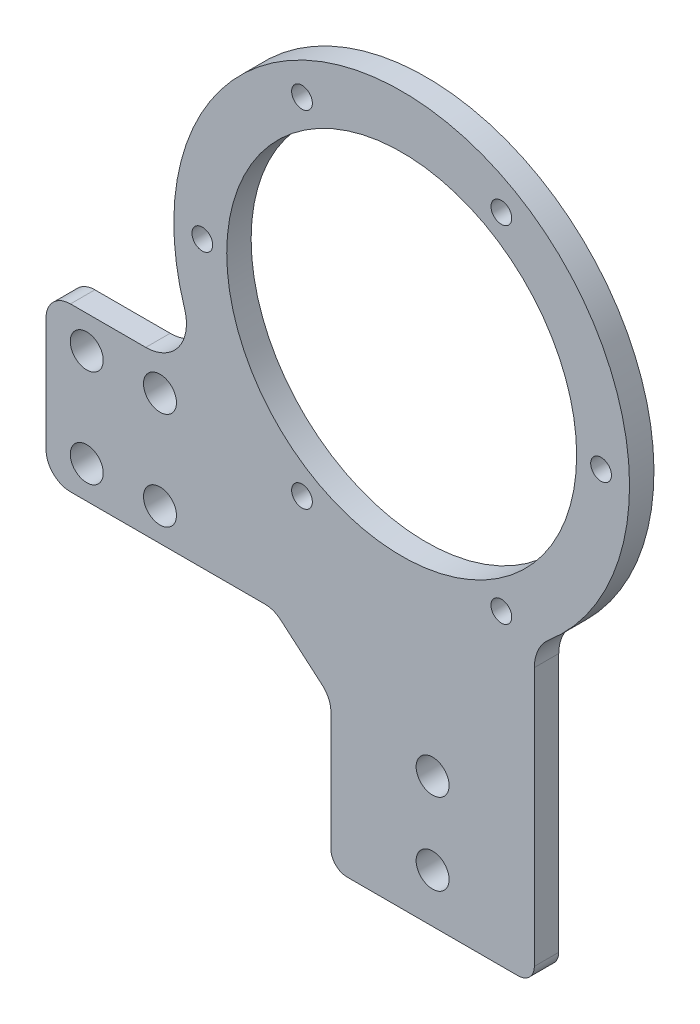
SolidWorks part; units mm, degrees
material "Thornel Mat VMA"
ref_plane "前视基准面" through (0, 0, 0) normal (0, 0, 1) x (1, 0, 0)
ref_plane "上视基准面" through (0, 0, 0) normal (0, 1, 0) x (1, 0, 0)
ref_plane "右视基准面" through (0, 0, 0) normal (1, 0, 0) x (0, 0, -1)
other "Configuration Table"
sketch "草图1" plane through (0, 0, 0) normal (0, 0, 1) x (1, 0, 0)
  line L0 (-35, 0) -> (0, 0)
  line L1 (0, 0) -> (0, -30)
  line L2 (0, -30) -> (25, -30)
  line L3 (25, -30) -> (25, 20)
  line L4 (25, 20) -> (-35, 20)
  line L5 (-35, 20) -> (-35, 0)
  dimension "D1" = 25
  dimension "D2" = 50
  dimension "D3" = 20
  dimension "D4" = 60
extrude "凸台-拉伸1" add sketch "草图1" along normal blind 3
sketch "草图2" plane through (0, 0, 0) normal (0, 0, -1) x (-1, 0, 0)
  line L0 (-25, -30) -> (-25, 20) construction
  line L1 (35, 0) -> (0, 0) construction
  circle A0 centre (-8.7, 35) radius 28
  dimension "D2" = 56
  dimension "D1" = 16.3
  dimension "D3" = 35
extrude "凸台-拉伸2" add sketch "草图2" against normal up to surface (3 mm away) up to face at (-3.3333, -3.3333, 3)
sketch "草图3" plane through (0, 0, 0) normal (0, 0, -1) x (-1, 0, 0)
  circle A0 centre (-8.7, 35) radius 21.5
  dimension "D1" = 43
extrude "切除-拉伸1" cut sketch "草图3" against normal up to surface (3 mm away) up to face at (-3.7039, 5.5146, 3)
fillet "圆角2" radius 5 2 edges at (25, 12.2336, 1.5) (-14.9432, 20, 1.5)
sketch "草图4" plane through (0, 0, 0) normal (0, 0, -1) x (-1, 0, 0)
  circle A10 centre (-33.2, 35) radius 1.275
  circle A16 centre (-8.7, 35) radius 24.5 construction
  circle A17 centre (-20.95, 56.2176) radius 1.275
  circle A18 centre (3.55, 56.2176) radius 1.275
  circle A19 centre (15.8, 35) radius 1.275
  circle A20 centre (3.55, 13.7824) radius 1.275
  circle A21 centre (-20.95, 13.7824) radius 1.275
  point P17 (-8.7, 35)
  dimension "D1" = 2.55
  dimension "D2" = 49
  dimension "D3" = 6
extrude "切除-拉伸2" cut sketch "草图4" against normal through all
sketch "草图5" plane through (0, 0, 0) normal (0, 0, -1) x (-1, 0, 0)
  line L0 (-12.5, -30) -> (-12.5, -13) construction
  line L1 (-17.5, -18) -> (-7.5, -18) construction
  line L2 (-17.5, -18) -> (-17.5, -8) construction
  line L3 (-17.5, -8) -> (-7.5, -8) construction
  line L4 (-7.5, -18) -> (-7.5, -8) construction
  line L5 (-17.5, -18) -> (-7.5, -8) construction
  line L6 (-17.5, -8) -> (-7.5, -18) construction
  line L7 (0, -30) -> (-25, -30) construction
  line L8 (35, 0) -> (0, 0) construction
  circle A4 centre (-12.5, -8) radius 2.025
  circle A5 centre (-12.5, -18) radius 2.025
  point P0 (-12.5, -13)
  dimension "D4" = 4.05
  dimension "D1" = 10
  dimension "D2" = 10
  dimension "D3" = 8
extrude "切除-拉伸3" cut sketch "草图5" against normal through all
sketch "草图6" plane through (0, 0, 0) normal (0, 0, -1) x (-1, 0, 0)
  line L0 (-25, -30) -> (-25, 9.7946) construction
  line L1 (-25, -24) -> (0, -24)
  line L2 (-25, -24) -> (-25, -30)
  line L3 (-25, -30) -> (0, -30)
  line L4 (0, -24) -> (0, -30)
  line L5 (0, 0) -> (0, -30) construction
  line L6 (0, -30) -> (-25, -30) construction
  dimension "D1" = 6
extrude "切除-拉伸4" cut sketch "草图6" against normal through all
fillet "圆角3" radius 2 2 edges at (0, -24, 1.5) (25, -24, 1.5)
sketch "草图8" plane through (0, 0, 3) normal (0, 0, 1) x (1, 0, 0)
  line L0 (-35, 20) -> (-35, 0) construction
  line L1 (-35, 10) -> (21.3095, 10) construction
  circle A0 centre (-30, 16) radius 2.025
  circle A1 centre (-30, 4) radius 2.025
  arc A2 (26.7727, 13.6136) -> (-17.9835, 26.5152) centre (8.7, 35) ccw construction
  dimension "D2" = 4.05
  dimension "D1" = 5
  dimension "D3" = 12
extrude "切除-拉伸5" cut sketch "草图8" against normal blind 10
sketch "草图9" plane through (0, 0, 0) normal (0, 0, -1) x (-1, 0, 0)
  line L1 (30, 16) -> (21, 16) construction
  line L2 (30, 16) -> (30, 4) construction
  line L3 (30, 4) -> (21, 4) construction
  line L4 (21, 16) -> (21, 4) construction
  circle A0 centre (30, 4) radius 2.025 construction
  circle A1 centre (21, 4) radius 2.025
  circle A2 centre (21, 16) radius 2.025
  dimension "D2" = 4.05
  dimension "D1" = 9
extrude "切除-拉伸6" cut sketch "草图9" against normal through all both
sketch "草图10" plane through (0, 0, 0) normal (0, 0, -1) x (-1, 0, 0)
  line L0 (0, -6) -> (7, 0)
  line L1 (0, 0) -> (0, -22) construction
  line L2 (35, 0) -> (0, 0) construction
  line L3 (7, 0) -> (0, 0)
  line L4 (0, 0) -> (0, -6)
  dimension "D1" = 6
  dimension "D2" = 7
extrude "凸台-拉伸3" add sketch "草图10" against normal up to surface (3 mm away) up to face at (-23.025, 4, 3)
fillet "圆角4" radius 3 4 edges at (-35, 0, 1.5) (-35, 20, 1.5) (-7, 0, 1.5) (0, -6, 1.5)
